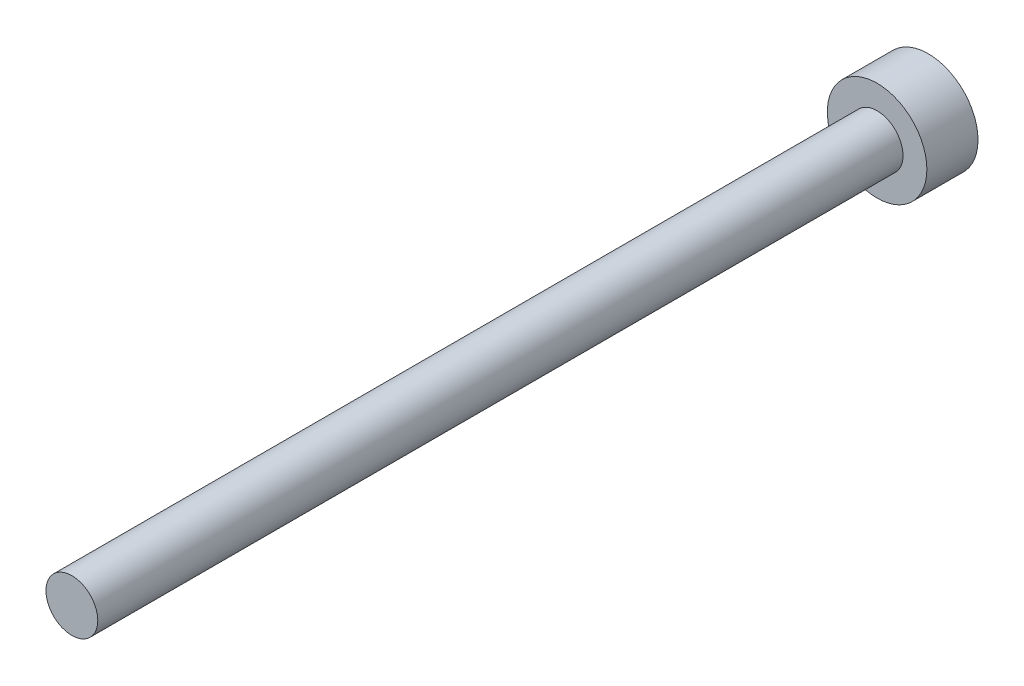
SolidWorks part; units mm, degrees
ref_plane "Front Plane" through (0, 0, 0) normal (0, 0, 1) x (1, 0, 0)
ref_plane "Top Plane" through (0, 0, 0) normal (0, 1, 0) x (1, 0, 0)
ref_plane "Right Plane" through (0, 0, 0) normal (1, 0, 0) x (0, 0, -1)
sketch "Sketch1" plane through (0, 0, 0) normal (0, 0, 1) x (1, 0, 0)
  circle A0 centre (0, 0) radius 0.9652
  dimension "D1" = 1.9304
extrude "Boss-Extrude1" add sketch "Sketch1" along normal blind 30
cosmetic thread "Cosmetic Thread1" parameters "D2"=0.9304
sketch "Sketch2" plane through (0, 0, 0) normal (0, 0, 1) x (1, 0, 0)
  circle A0 centre (0, 0) radius 1.8542
  dimension "D1" = 3.7084
extrude "Boss-Extrude2" add sketch "Sketch2" against normal blind 1.905
sketch "Sketch3" plane through (0, 0, -1.905) normal (0, 0, -1) x (-1, 0, 0)
  line L0 (2.0396, 0) -> (-2.0396, 0) construction
  line L1 (0.8506, 0) -> (0.4253, 0.7366)
  line L2 (0.4253, 0.7366) -> (-0.4253, 0.7366)
  line L3 (-0.4253, 0.7366) -> (-0.8506, 0)
  line L4 (-0.8506, 0) -> (-0.4253, -0.7366)
  line L5 (-0.4253, -0.7366) -> (0.4253, -0.7366)
  line L6 (0.4253, -0.7366) -> (0.8506, 0)
  circle A0 centre (0, 0) radius 0.7366 construction
  dimension "D1" = 1.4732
extrude "Cut-Extrude1" cut sketch "Sketch3" against normal blind 1.524
